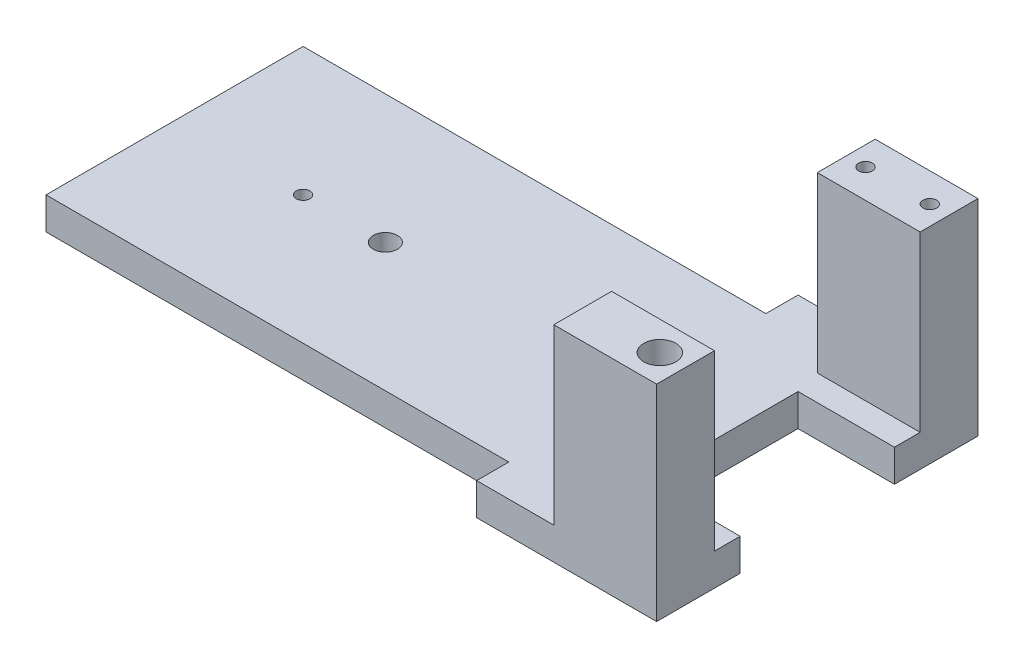
SolidWorks part; units mm, degrees
ref_plane "Front Plane" through (0, 0, 0) normal (0, 0, 1) x (1, 0, 0)
ref_plane "Top Plane" through (0, 0, 0) normal (0, 1, 0) x (1, 0, 0)
ref_plane "Right Plane" through (0, 0, 0) normal (1, 0, 0) x (0, 0, -1)
sketch "Sketch2" plane through (0, 0, 0) normal (0, 1, 0) x (1, 0, 0)
  line L0 (91.44, 6.35) -> (127, 6.35)
  line L1 (127, 6.35) -> (127, 69.85)
  line L2 (127, 69.85) -> (91.44, 69.85)
  line L3 (0, 63.5) -> (0, 12.7)
  line L4 (0, 63.5) -> (91.44, 63.5)
  line L5 (91.44, 63.5) -> (91.44, 69.85)
  line L6 (0, 38.1) -> (88.4688, 38.1) construction
  line L7 (91.44, 12.7) -> (91.44, 6.35)
  line L8 (0, 12.7) -> (91.44, 12.7)
  dimension "D1" = 127
  dimension "D2" = 63.5
  dimension "D3" = 25.4
  dimension "D4" = 91.44
  dimension "D5" = 12.7
  dimension "D6" = 127
extrude "Boss-Extrude3" add sketch "Sketch2" against normal blind 6.35
sketch "Sketch4" plane through (0, 0, 0) normal (0, 1, 0) x (1, 0, 0)
  line L0 (127, 69.85) -> (106.68, 69.85)
  line L2 (127, 17.78) -> (127, 6.35)
  line L3 (106.68, 58.42) -> (127, 58.42)
  line L4 (127, 6.35) -> (127, 69.85) construction
  line L5 (127, 58.42) -> (127, 69.85)
  line L6 (106.68, 17.78) -> (127, 17.78)
  line L7 (106.68, 69.85) -> (106.68, 58.42)
  line L10 (106.68, 6.35) -> (106.68, 17.78)
  line L11 (127, 6.35) -> (106.68, 6.35)
  line L13 (127, 38.1) -> (0, 38.1) construction
  line L14 (0, 63.5) -> (0, 12.7) construction
  dimension "D1" = 11.43
  dimension "D2" = 20.32
extrude "Boss-Extrude4" add sketch "Sketch4" along normal blind 34.29
sketch "Sketch5" plane through (0, 0, 0) normal (0, 1, 0) x (1, 0, 0)
  line L0 (127, 53.34) -> (107.95, 53.34)
  line L1 (127, 17.78) -> (127, 58.42) construction
  line L2 (107.95, 53.34) -> (107.95, 22.86)
  line L3 (107.95, 22.86) -> (127, 22.86)
  line L4 (127, 22.86) -> (127, 53.34)
  point P4 (127, 38.1)
  dimension "D1" = 15.24
  dimension "D2" = 19.05
  dimension "D3" = 30.48
extrude "Cut-Extrude1" cut sketch "Sketch5" against normal blind 12.7
hole_wizard "3/16 (0.1875) Dowel Hole4" positions "Sketch23" profile "Sketch20" hole size "3/16" standard "ANSI Inch" end condition through all
sketch "Sketch23" plane through (0, 0, 0) normal (0, 1, 0) x (1, 0, 0)
  line L0 (127, 53.34) -> (127, 58.42) construction
  line L1 (0, 12.7) -> (91.44, 12.7) construction
  point P0 (41.656, 38.1)
  dimension "D1" = 85.344
  dimension "D2" = 25.4
sketch "Sketch20" plane through (41.656, 0, -38.1) normal (1, 0, 0) x (0, 0, 1)
  line L0 (0, 0) -> (0, 6.35)
  line L1 (0, 6.35) -> (2.3812, 6.35)
  line L2 (2.3812, 6.35) -> (2.3812, 0)
  line L5 (2.3812, 0) -> (0, 0)
  line L11 (0, -6.35) -> (0, 107.95) construction
  dimension "Thru Hole Dia." = 4.7625
  dimension "Thru Hole Depth" = 6.35
hole_wizard "1/4 (0.2500) Dowel Hole1" positions "Sketch32" profile "Sketch31" hole size "1/4" standard "ANSI Inch" end condition through all
sketch "Sketch32" plane through (0, 34.29, 0) normal (0, 1, 0) x (1, 0, 0)
  line L2 (127, 6.35) -> (127, 17.78) construction
  line L3 (106.68, 6.35) -> (127, 6.35) construction
  point P2 (121.92, 12.065)
  dimension "D3" = 5.08
  dimension "D4" = 5.715
sketch "Sketch31" plane through (121.92, 34.29, -12.065) normal (1, 0, 0) x (0, 0, 1)
  line L0 (0, 0) -> (0, 40.64)
  line L1 (0, 40.64) -> (3.175, 40.64)
  line L2 (3.175, 40.64) -> (3.175, 0)
  line L5 (3.175, 0) -> (0, 0)
  line L11 (0, -6.35) -> (0, 107.95) construction
  dimension "Thru Hole Dia." = 6.35
  dimension "Thru Hole Depth" = 40.64
hole_wizard "#36 (0.1065) Diameter Hole1" positions "Sketch34" profile "Sketch33" hole size "#36" standard "ANSI Inch" end condition through all
sketch "Sketch34" plane through (0, 0, 0) normal (0, 1, 0) x (1, 0, 0)
  line L0 (0, 63.5) -> (0, 12.7) construction
  line L1 (91.44, 63.5) -> (0, 63.5) construction
  point P0 (25.4, 38.1)
  point P2 (79.375, 38.1)
  dimension "D1" = 25.4
  dimension "D2" = 79.375
  dimension "D3" = 25.4
  dimension "D4" = 25.4
sketch "Sketch33" plane through (25.4, 0, -38.1) normal (1, 0, 0) x (0, 0, 1)
  line L0 (0, 0) -> (0, 6.35)
  line L1 (0, 6.35) -> (1.3525, 6.35)
  line L2 (1.3525, 6.35) -> (1.3525, 0)
  line L5 (1.3525, 0) -> (0, 0)
  line L11 (0, -6.35) -> (0, 107.95) construction
  dimension "Thru Hole Dia." = 2.7051
  dimension "Thru Hole Depth" = 6.35
hole_wizard "#6-32 Tapped Hole1" positions "Sketch36" profile "Sketch35" tap size "#6-32" standard "ANSI Inch" end condition through all
sketch "Sketch36" plane through (0, 34.29, 0) normal (0, 1, 0) x (1, 0, 0)
  line L0 (127, 64.135) -> (106.68, 64.135) construction
  line L1 (127, 58.42) -> (127, 69.85) construction
  line L2 (106.68, 69.85) -> (106.68, 58.42) construction
  point P0 (123.19, 64.135)
  point P2 (110.49, 64.135)
  dimension "D1" = 3.81
  dimension "D2" = 3.81
sketch "Sketch35" plane through (123.19, 34.29, -64.135) normal (1, 0, 0) x (0, 0, 1)
  line L0 (0, 0) -> (0, 40.64)
  line L1 (0, 40.64) -> (1.3525, 40.64)
  line L2 (1.3525, 40.64) -> (1.3525, 0)
  line L5 (1.3525, 0) -> (0, 0)
  line L11 (0, -6.35) -> (0, 107.95) construction
  dimension "Thread Major Dia." = 2.7051
  dimension "Thru Tap Drill Depth" = 40.64
